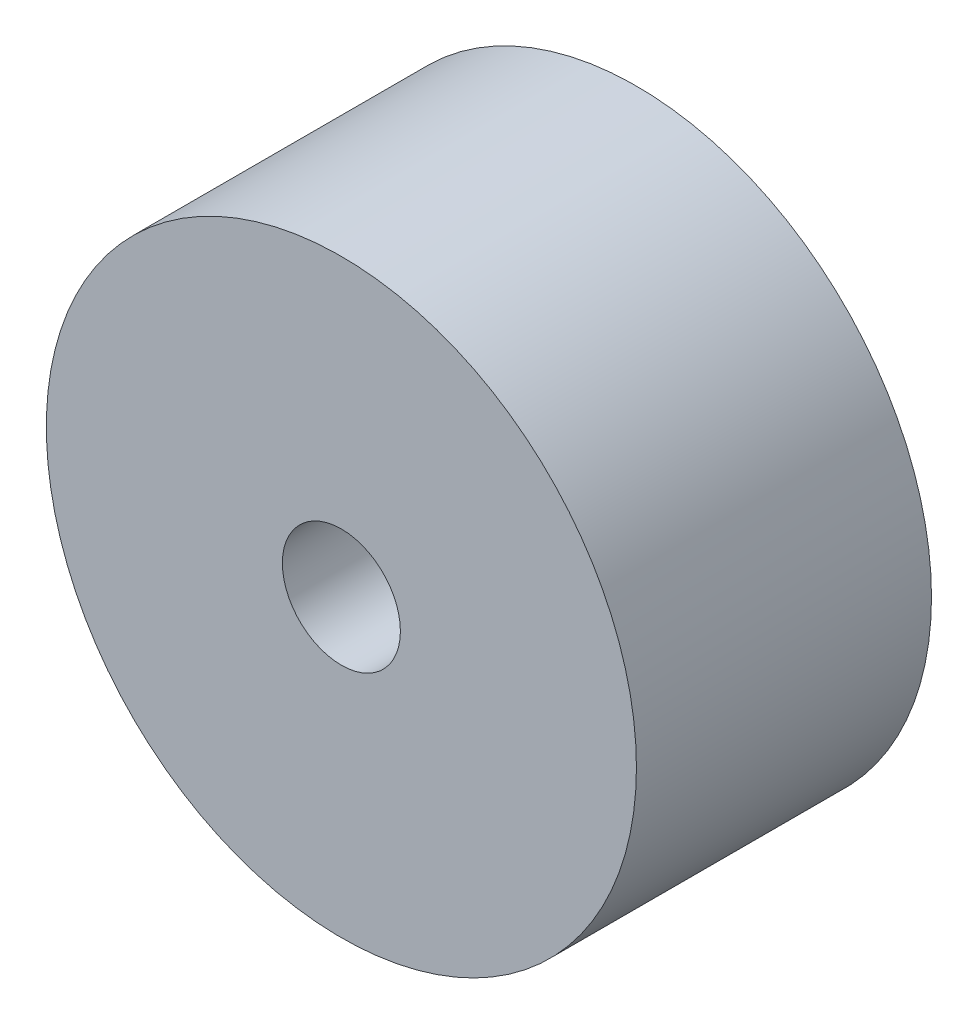
SolidWorks part; units mm, degrees
ref_plane "Front Plane" through (0, 0, 0) normal (0, 0, 1) x (1, 0, 0)
ref_plane "Top Plane" through (0, 0, 0) normal (0, 1, 0) x (1, 0, 0)
ref_plane "Right Plane" through (0, 0, 0) normal (1, 0, 0) x (0, 0, -1)
sketch "Croquis1" plane through (0, 0, 0) normal (0, 0, 1) x (1, 0, 0)
  circle A0 centre (0, 0) radius 0.1
  circle A1 centre (0, 0) radius 0.5
  dimension "D1" = 0.2
  dimension "D2" = 1
extrude "Saliente-Extruir1" add sketch "Croquis1" along normal blind 0.5
sketch "Croquis2" plane through (0, 0, 0) normal (1, 0, 0) x (0, 0, -1)
  line L0 (0, 0) -> (-0.125, 0)
  line L1 (0, 0) -> (0, -0.2795)
  line L2 (0, -0.5) -> (0, 0.5) construction
  arc A0 (-0.125, 0) -> (0, -0.2795) centre (0.25, 0) ccw
  dimension "D1" = 0.75
  dimension "D2" = 0.25
revolve "Cortar-Revolución1" cut sketch "Croquis2" angle 360 about L0
fillet "Redondeo1" radius 0.15 1 edges at (-0.1, 0, 0.1114)
